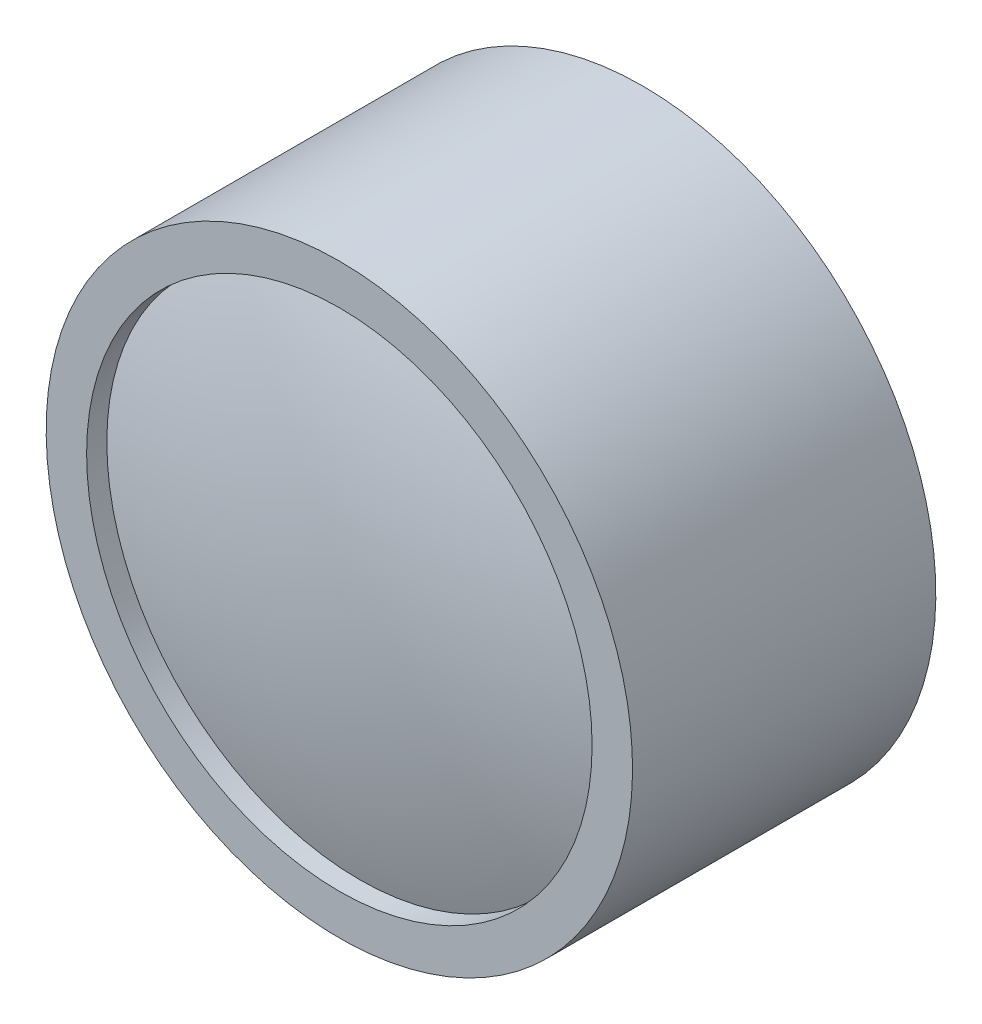
SolidWorks part; units mm, degrees
ref_plane "Front Plane" through (0, 0, 0) normal (0, 0, 1) x (1, 0, 0)
ref_plane "Top Plane" through (0, 0, 0) normal (0, 1, 0) x (1, 0, 0)
ref_plane "Right Plane" through (0, 0, 0) normal (1, 0, 0) x (0, 0, -1)
sketch "Sketch1" plane through (0, 0, 0) normal (1, 0, 0) x (0, 0, -1)
  line L0 (0, 0) -> (0, 14.5)
  line L1 (0, 14.5) -> (-15, 14.5)
  line L2 (-15, 14.5) -> (-15, 12.5)
  line L3 (-15, 12.5) -> (-14, 12.5)
  line L4 (0, 0) -> (-16, 0)
  arc A0 (-14, 12.5) -> (-16, 0) centre (24.0625, 0) ccw
  dimension "D1" = 1
  dimension "D2" = 14.5
  dimension "D3" = 2
  dimension "D4" = 1
  dimension "D5" = 15
revolve "Revolve1" add sketch "Sketch1" angle 360 about L4
